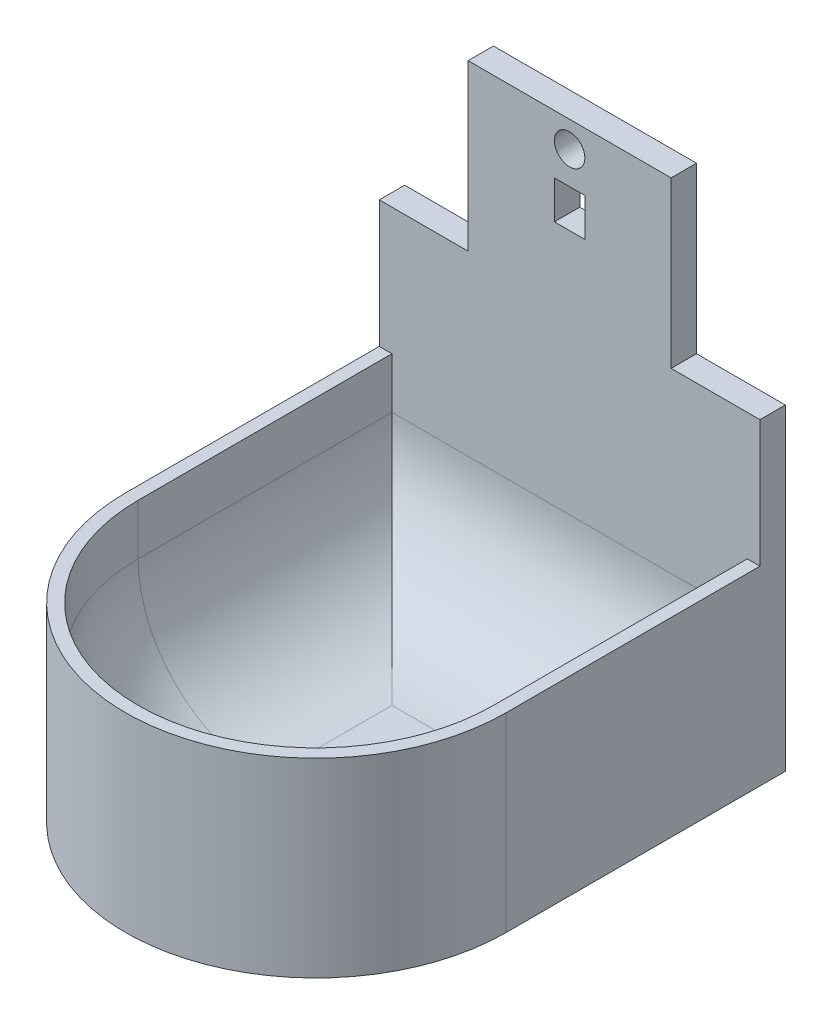
SolidWorks part; units mm, degrees
material "ABS"
ref_plane "Front Plane" through (0, 0, 0) normal (0, 0, 1) x (1, 0, 0)
ref_plane "Top Plane" through (0, 0, 0) normal (0, 1, 0) x (1, 0, 0)
ref_plane "Right Plane" through (0, 0, 0) normal (1, 0, 0) x (0, 0, -1)
sketch "Sketch1" plane through (0, 0, 0) normal (0, 1, 0) x (1, 0, 0)
  line L1 (0, 0) -> (38.1, 0)
  line L2 (0, 0) -> (0, -25.4)
  line L4 (38.1, 0) -> (38.1, -25.4)
  arc A0 (0, -25.4) -> (38.1, -25.4) centre (19.05, -25.4) ccw
  dimension "D1" = 38.1
  dimension "D2" = 25.4
extrude "Boss-Extrude1" add sketch "Sketch1" along normal blind 1.27
sketch "Sketch3" plane through (0, 1.27, 0) normal (0, 1, 0) x (1, 0, 0)
  line L0 (0, 0) -> (0, -25.4) construction
  line L1 (38.1, -25.4) -> (38.1, 0) construction
  line L2 (0, 0) -> (0, -25.4)
  line L3 (38.1, -25.4) -> (38.1, 0)
  line L4 (0, 0) -> (1.27, 0)
  line L5 (38.1, 0) -> (36.83, 0)
  line L6 (1.27, 0) -> (1.27, -25.4)
  line L7 (36.83, 0) -> (36.83, -25.4)
  arc A0 (0, -25.4) -> (38.1, -25.4) centre (19.05, -25.4) ccw construction
  arc A1 (0, -25.4) -> (38.1, -25.4) centre (19.05, -25.4) ccw
  arc A2 (1.27, -25.4) -> (36.83, -25.4) centre (19.05, -25.4) ccw
  dimension "D1" = 25.4
  dimension "D2" = 1.27
extrude "Boss-Extrude3" add sketch "Sketch3" along normal blind 17.78
sketch "Sketch5" plane through (0, 0, 0) normal (0, 0, -1) x (-1, 0, 0)
  line L1 (-38.1, 19.05) -> (0, 19.05)
  line L2 (-38.1, 19.05) -> (-38.1, 0)
  line L3 (-38.1, 0) -> (0, 0)
  line L4 (0, 19.05) -> (0, 0)
extrude "Boss-Extrude4" add sketch "Sketch5" along normal blind 2.54
sketch "Sketch4" plane through (38.1, 0, 0) normal (1, 0, 0) x (0, 0, -1)
  line L1 (-2.54, 19.05) -> (0, 19.05)
  line L2 (-2.54, 19.05) -> (-2.54, 16.51)
  line L3 (-2.54, 16.51) -> (0, 16.51)
  line L4 (0, 19.05) -> (0, 16.51)
  line L5 (2.54, 19.05) -> (2.54, 0) construction
  dimension "D1" = 2.54
  dimension "D2" = 2.54
  dimension "D3" = 2.54
extrude "Cut-Extrude1" [suppressed] cut sketch "Sketch4" against normal through all
fillet "Fillet1" radius 12.7 4 edges at (19.05, 1.27, 43.18)
sketch "Sketch7" [suppressed] plane through (0, 0, 0) normal (0, 0, 1) x (1, 0, 0)
  line L0 (38.1, 19.05) -> (0, 19.05) construction
  circle A0 centre (19.05, 19.05) radius 15.24
  dimension "D1" = 30.48
extrude "Cut-Extrude3" [suppressed] cut sketch "Sketch7" along normal through all
sketch "Sketch9" plane through (0, 0, 0) normal (-1, 0, 0) x (0, 0, 1)
  line L0 (24.13, 19.05) -> (26.67, 19.05) construction
  line L1 (24.13, 34.29) -> (26.67, 34.29)
  line L2 (24.13, 3.81) -> (26.67, 3.81)
  arc A0 (24.13, 34.29) -> (24.13, 3.81) centre (24.13, 19.05) ccw
  arc A1 (26.67, 3.81) -> (26.67, 34.29) centre (26.67, 19.05) ccw
  point P2 (25.4, 19.05)
  dimension "D1" = 15.24
  dimension "D2" = 2.54
extrude "Cut-Extrude5" [suppressed] cut sketch "Sketch9" against normal up to next
fillet "Fillet3" [suppressed] radius 2.54
sketch "Sketch10" plane through (0, 0, -2.54) normal (0, 0, -1) x (-1, 0, 0)
  line L0 (-29.21, 31.75) -> (-29.21, 48.26)
  line L1 (-29.21, 48.26) -> (-8.89, 48.26)
  line L2 (-8.89, 48.26) -> (-8.89, 31.75)
  line L3 (-8.89, 31.75) -> (0, 31.75)
  line L4 (0, 31.75) -> (0, 19.05)
  line L5 (0, 19.05) -> (-38.1, 19.05)
  line L6 (-38.1, 19.05) -> (-38.1, 31.75)
  line L7 (-38.1, 31.75) -> (-29.21, 31.75)
  line L8 (-19.05, 48.26) -> (-19.05, 19.05) construction
  dimension "D1" = 12.7
  dimension "D2" = 16.51
  dimension "D3" = 38.1
  dimension "D4" = 8.89
extrude "Boss-Extrude5" add sketch "Sketch10" against normal blind 2.54
sketch "Sketch12" plane through (0, 0, -2.54) normal (0, 0, -1) x (-1, 0, 0)
  line L0 (-20.574, 42.418) -> (-17.526, 42.418)
  line L1 (-20.574, 42.418) -> (-20.574, 38.608)
  line L2 (-20.574, 38.608) -> (-17.526, 38.608)
  line L3 (-17.526, 42.418) -> (-17.526, 38.608)
  line L4 (-8.89, 48.26) -> (-29.21, 48.26) construction
  circle A0 centre (-19.05, 45.6565) radius 1.524
  point P6 (-19.05, 42.418)
  point P7 (-19.05, 48.26)
  dimension "D4" = 3.048
  dimension "D1" = 3.2385
  dimension "D2" = 3.048
  dimension "D3" = 3.81
  dimension "D5" = 2.6035
extrude "Cut-Extrude6" cut sketch "Sketch12" against normal up to next
